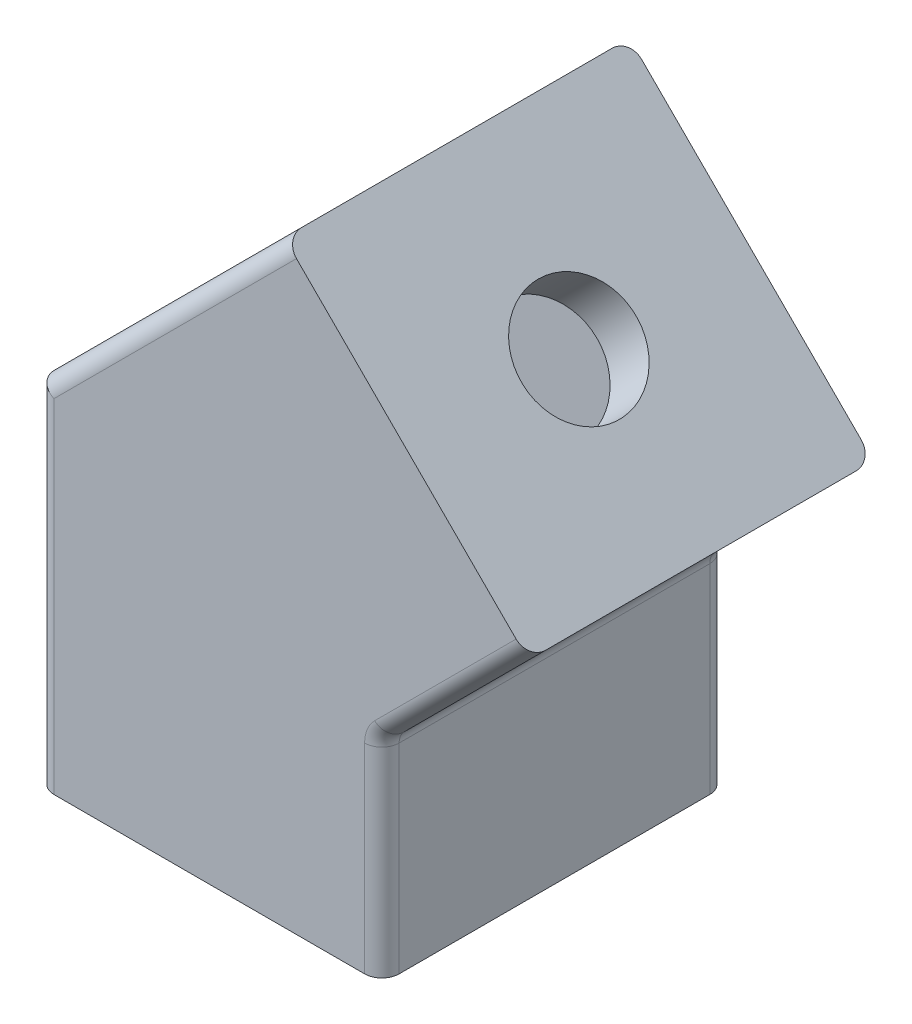
SolidWorks part; units mm, degrees
material "6063-T6"
ref_plane "Front Plane" through (0, 0, 0) normal (0, 0, 1) x (1, 0, 0)
ref_plane "Top Plane" through (0, 0, 0) normal (0, 1, 0) x (1, 0, 0)
ref_plane "Right Plane" through (0, 0, 0) normal (1, 0, 0) x (0, 0, -1)
sketch "Sketch1" plane through (0, 0, 0) normal (0, 0, 1) x (1, 0, 0)
  line L0 (0, -24) -> (0, 0)
  line L1 (0, 0) -> (16.9706, 16.9706)
  line L2 (16.9706, 16.9706) -> (-11.3137, 45.2548)
  line L3 (-11.3137, 45.2548) -> (-40, 16.5685)
  line L4 (-40, 16.5685) -> (-40, -24)
  line L5 (-40, -24) -> (0, -24)
  dimension "D1" = 45
  dimension "D2" = 40
  dimension "D3" = 24
extrude "Boss-Extrude1" add sketch "Sketch1" along normal mid plane 40
shell "Shell1" thickness 3.3
sketch "Sketch2" plane through (0, -24, 0) normal (0, -1, 0) x (1, 0, 0)
  line L0 (-40, -20) -> (0, 20) construction
  circle A0 centre (-20, 0) radius 6.65
  dimension "D1" = 13.3
extrude "Cut-Extrude1" cut sketch "Sketch2" against normal up to next
sketch "Sketch3" plane through (16.9706, 16.9706, 0) normal (0.7071, 0.7071, 0) x (0, 0, -1)
  line L0 (-20, 0) -> (20, 40) construction
  circle A0 centre (0, 20) radius 6.65
  dimension "D1" = 13.3
extrude "Cut-Extrude2" cut sketch "Sketch3" against normal up to next
fillet "Fillet1" radius 2 10 edges at (8.4853, 8.4853, -20) (-3.3, 1.3669, 0) (-25.6569, 30.9117, 20) (-40, -3.7157, 20) (-25.6569, 30.9117, -20) (-40, -3.7157, -20) (0, -12, -20) (0, 0, 0) (0, -12, 20) (8.4853, 8.4853, 20)
